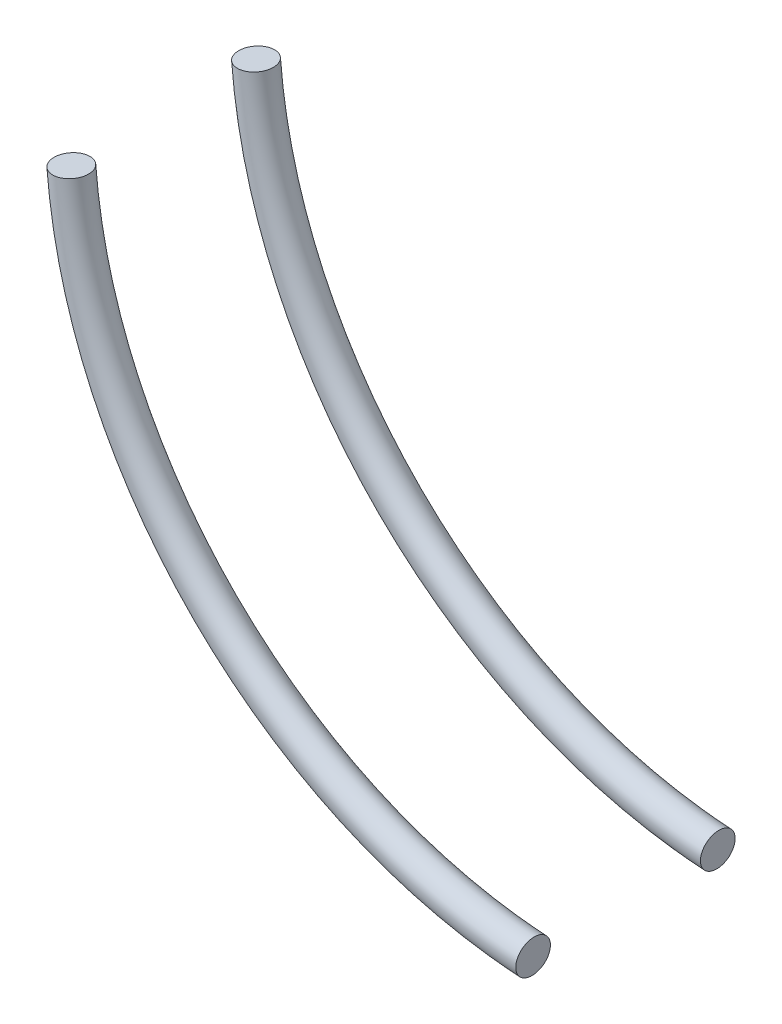
SolidWorks part; units mm, degrees
ref_plane "前基準面" through (0, 0, 0) normal (0, 0, 1) x (1, 0, 0)
ref_plane "上基準面" through (0, 0, 0) normal (0, 1, 0) x (1, 0, 0)
ref_plane "右基準面" through (0, 0, 0) normal (1, 0, 0) x (0, 0, -1)
sketch "草圖1" plane through (0, 0, 0) normal (0, 0, 1) x (1, 0, 0)
  line L1 (0, 0) -> (20, 0) construction
  line L2 (0, 0) -> (0, 20) construction
  line L3 (0, 20) -> (20, 20) construction
  line L4 (20, 0) -> (20, 20) construction
  arc A0 (0, 20) -> (20, 0.3466) centre (21.3145, 21.6873) ccw
  point P7 (0, 0)
  dimension "D1" = 20
  dimension "D2" = 20
ref_plane "平面1" through (0, 20, 0) normal (0.0789, -0.9969, 0) x (-0.9969, -0.0789, 0)
sketch "草圖2" plane through (0, 20, 0) normal (0.0789, -0.9969, 0) x (-0.9969, -0.0789, 0)
  line L0 (0, 4) -> (0, -4) construction
  circle A0 centre (0, 4) radius 0.75
  circle A1 centre (0, -4) radius 0.75
  point P4 (0.7918, -2.6032)
  point P5 (0, 0)
  dimension "D1" = 1.5
  dimension "D2" = 8
sweep "掃出1" add profiles "草圖2" path "草圖1"
